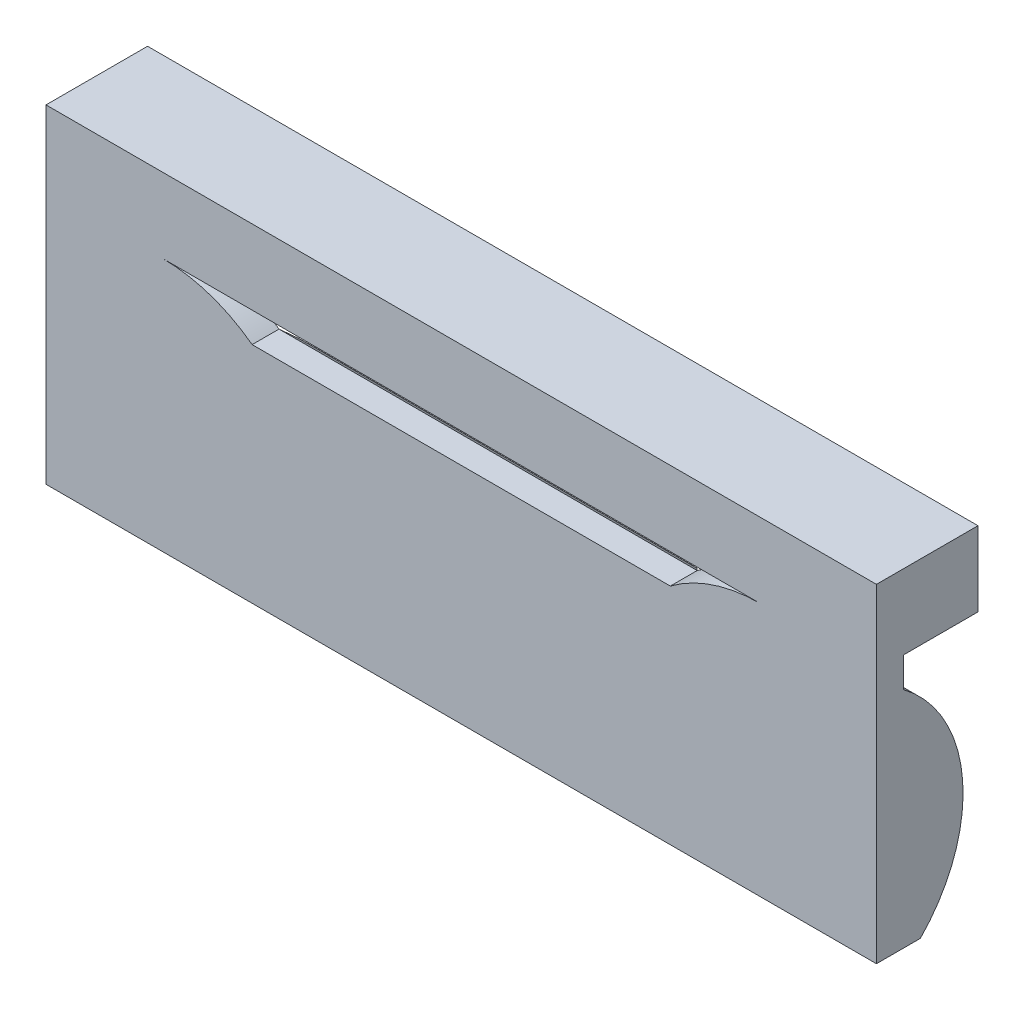
SolidWorks part; units mm, degrees
ref_plane "Front Plane" through (0, 0, 0) normal (0, 0, 1) x (1, 0, 0)
ref_plane "Top Plane" through (0, 0, 0) normal (0, 1, 0) x (1, 0, 0)
ref_plane "Right Plane" through (0, 0, 0) normal (1, 0, 0) x (0, 0, -1)
sketch "Sketch1" plane through (0, 0, 0) normal (0, 0, 1) x (1, 0, 0)
  line L0 (-6.95, 2.25) -> (-6.95, -2.25)
  line L1 (6.5, 2.25) -> (-6.5, 2.25)
  line L2 (6.5, 2.25) -> (6.5, -2.25)
  line L3 (6.5, -2.25) -> (-6.5, -2.25)
  line L4 (-6.5, 2.25) -> (-6.5, -2.25)
  line L5 (6.5, 2.25) -> (-6.5, -2.25) construction
  line L6 (6.5, -2.25) -> (-6.5, 2.25) construction
  line L7 (6.95, 2.25) -> (6.95, -2.25)
  line L8 (6.5, 2.75) -> (-6.5, 2.75)
  line L9 (6.5, -2.75) -> (-6.5, -2.75)
  line L10 (-6.95, 2.25) -> (-6.95, 2.75)
  line L11 (-6.95, 2.75) -> (-6.5, 2.75)
  line L12 (-6.95, -2.25) -> (-6.95, -2.75)
  line L13 (-6.95, -2.75) -> (-6.5, -2.75)
  line L14 (6.5, -2.75) -> (6.95, -2.75)
  line L15 (6.95, -2.75) -> (6.95, -2.25)
  line L16 (6.95, 2.25) -> (6.95, 2.75)
  line L17 (6.95, 2.75) -> (6.5, 2.75)
  line L18 (-5, 1.5) -> (5, 1.5)
  line L20 (-5.835, -2.0198) -> (-5.835, -2.25) construction
  line L21 (0, 2.25) -> (0, -2.25) construction
  line L23 (5.835, 1) -> (5.835, -2.25) construction
  line L24 (-6.5, 1.875) -> (-6.5, 1)
  line L30 (6.5, 1.875) -> (6.5, 1)
  arc A0 (-5, 1.5) -> (-2.8349, -2.25) centre (-5, -1) cw
  arc A1 (5, 1.5) -> (2.8349, -2.25) centre (5, -1) ccw
  point P0 (0, 0)
  point P21 (-4.0978, -2.25)
  point P26 (0, 0)
  dimension "D10" = 2.5
  dimension "D1" = 13
  dimension "D2" = 4.5
  dimension "D7" = 0.75
  dimension "D8" = 10
  dimension "D9" = 0.665
  dimension "D3" = 0.45
  dimension "D4" = 0.45
  dimension "D5" = 0.5
  dimension "D6" = 0.5
extrude "Boss-Extrude1" add sketch "Sketch1" along normal mid plane 0.45 contours L16 L17 L8 L11 L10 L0 L12 L13 L9 L14 L15 L7 L4 L1 L2 L3 | L18 A1 L3 L2 L1 L4 A0 | A1 L18 A0 L3
sketch "Sketch2" plane through (0, 0, -0.225) normal (0, 0, -1) x (-1, 0, 0)
  line L0 (-6.5, 1.875) -> (-6.5, 1) construction
  line L1 (6.5, 1.875) -> (6.5, 1) construction
  line L2 (5, 1.5) -> (-5, 1.5) construction
  line L3 (-6.5, 1.875) -> (-6.5, 1)
  line L4 (6.5, 2.25) -> (-6.5, 2.25)
  line L5 (6.5, -2.25) -> (6.5, 2.25)
  line L6 (-6.5, -2.25) -> (6.5, -2.25)
  line L7 (-6.5, 2.25) -> (-6.5, -2.25)
  line L8 (6.5, 2.25) -> (-6.5, 2.25)
  line L9 (6.5, -2.25) -> (6.5, 2.25)
  line L10 (-6.5, -2.25) -> (6.5, -2.25)
  line L11 (-6.5, 2.25) -> (-6.5, -2.25)
  line L12 (6.5, 1.875) -> (6.5, 1)
  line L13 (5, 1.5) -> (-5, 1.5)
  line L20 (-6.95, -2.25) -> (-6.95, -2.75)
  line L21 (-6.95, 2.25) -> (-6.95, -2.25)
  line L22 (-6.95, 2.75) -> (-6.95, 2.25)
  line L23 (-6.5, 2.75) -> (-6.95, 2.75)
  line L24 (6.5, 2.75) -> (-6.5, 2.75)
  line L25 (6.95, 2.75) -> (6.5, 2.75)
  line L26 (6.95, 2.25) -> (6.95, 2.75)
  line L27 (6.95, -2.25) -> (6.95, 2.25)
  line L28 (6.95, -2.75) -> (6.95, -2.25)
  line L29 (6.5, -2.75) -> (6.95, -2.75)
  line L30 (-6.5, -2.75) -> (6.5, -2.75)
  line L31 (-6.95, -2.75) -> (-6.5, -2.75)
  line L32 (-6.95, -2.25) -> (-6.95, -2.75)
  line L33 (-6.95, 2.25) -> (-6.95, -2.25)
  line L34 (-6.95, 2.75) -> (-6.95, 2.25)
  line L35 (-6.5, 2.75) -> (-6.95, 2.75)
  line L36 (6.5, 2.75) -> (-6.5, 2.75)
  line L37 (6.95, 2.75) -> (6.5, 2.75)
  line L38 (6.95, 2.25) -> (6.95, 2.75)
  line L39 (6.95, -2.25) -> (6.95, 2.25)
  line L40 (6.95, -2.75) -> (6.95, -2.25)
  line L41 (6.5, -2.75) -> (6.95, -2.75)
  line L42 (-6.5, -2.75) -> (6.5, -2.75)
  line L43 (-6.95, -2.75) -> (-6.5, -2.75)
  arc A0 (-2.8349, -2.25) -> (-5, 1.5) centre (-5, -1) ccw construction
  arc A1 (5, 1.5) -> (2.8349, -2.25) centre (5, -1) ccw construction
  arc A2 (-2.8349, -2.25) -> (-5, 1.5) centre (-5, -1) ccw
  arc A3 (5, 1.5) -> (2.8349, -2.25) centre (5, -1) ccw
  line M17 (-6.95, 2.75) -> (-6.95, -2.75)
  line M18 (-6.95, -2.75) -> (6.95, -2.75)
  line M19 (6.95, -2.75) -> (6.95, 2.75)
  line M20 (6.95, 2.75) -> (-6.95, 2.75)
  dimension "D1" = 0
  dimension "D2" = 0
extrude "Boss-Extrude2" add sketch "Sketch2" along normal blind 1.25 contours L11 L8 L9 L10 L3 M20 M17 M18 M19
sketch "Sketch3" plane through (0, 0, -0.225) normal (0, 0, -1) x (-1, 0, 0)
  line L0 (-6.5, 1.875) -> (-6.5, 1) construction
  line L1 (6.5, 1.875) -> (6.5, 1) construction
  line L2 (5, 1.5) -> (-5, 1.5) construction
  line L3 (-6.5, 1.875) -> (-6.5, 1)
  line L4 (6.5, 2.25) -> (-6.5, 2.25)
  line L5 (6.5, -2.25) -> (6.5, 2.25)
  line L6 (-6.5, -2.25) -> (6.5, -2.25)
  line L7 (-6.5, 2.25) -> (-6.5, -2.25)
  line L8 (6.5, 2.25) -> (-6.5, 2.25)
  line L9 (6.5, -2.25) -> (6.5, 2.25)
  line L10 (-6.5, -2.25) -> (6.5, -2.25)
  line L11 (-6.5, 2.25) -> (-6.5, -2.25)
  line L12 (6.5, 1.875) -> (6.5, 1)
  line L13 (5, 1.5) -> (-5, 1.5)
  line L20 (-6.95, -2.25) -> (-6.95, -2.75)
  line L21 (-6.95, 2.25) -> (-6.95, -2.25)
  line L22 (-6.95, 2.75) -> (-6.95, 2.25)
  line L23 (-6.5, 2.75) -> (-6.95, 2.75)
  line L24 (6.5, 2.75) -> (-6.5, 2.75)
  line L25 (6.95, 2.75) -> (6.5, 2.75)
  line L26 (6.95, 2.25) -> (6.95, 2.75)
  line L27 (6.95, -2.25) -> (6.95, 2.25)
  line L28 (6.95, -2.75) -> (6.95, -2.25)
  line L29 (6.5, -2.75) -> (6.95, -2.75)
  line L30 (-6.5, -2.75) -> (6.5, -2.75)
  line L31 (-6.95, -2.75) -> (-6.5, -2.75)
  line L32 (-6.95, -2.25) -> (-6.95, -2.75)
  line L33 (-6.95, 2.25) -> (-6.95, -2.25)
  line L34 (-6.95, 2.75) -> (-6.95, 2.25)
  line L35 (-6.5, 2.75) -> (-6.95, 2.75)
  line L36 (6.5, 2.75) -> (-6.5, 2.75)
  line L37 (6.95, 2.75) -> (6.5, 2.75)
  line L38 (6.95, 2.25) -> (6.95, 2.75)
  line L39 (6.95, -2.25) -> (6.95, 2.25)
  line L40 (6.95, -2.75) -> (6.95, -2.25)
  line L41 (6.5, -2.75) -> (6.95, -2.75)
  line L42 (-6.5, -2.75) -> (6.5, -2.75)
  line L43 (-6.95, -2.75) -> (-6.5, -2.75)
  arc A0 (-2.8349, -2.25) -> (-5, 1.5) centre (-5, -1) ccw construction
  arc A1 (5, 1.5) -> (2.8349, -2.25) centre (5, -1) ccw construction
  arc A2 (-2.8349, -2.25) -> (-5, 1.5) centre (-5, -1) ccw
  arc A3 (5, 1.5) -> (2.8349, -2.25) centre (5, -1) ccw
  dimension "D1" = 0
  dimension "D2" = 0
extrude "Boss-Extrude3" add sketch "Sketch3" along normal blind 2 contours A3 L13 A2 L10
sketch "Sketch4" plane through (0, 0, -2.225) normal (0, 0, -1) x (-1, 0, 0)
  line L0 (5, 1.5) -> (-5, 1.5) construction
  line L1 (3.5, -2.25) -> (-3.5, -2.25)
  line L2 (3.5, -2.25) -> (3.5, 2.25)
  line L3 (3.5, 2.25) -> (-3.5, 2.25)
  line L4 (-3.5, -2.25) -> (-3.5, 2.25)
  line L5 (3.5, -2.25) -> (-3.5, 2.25) construction
  line L6 (3.5, 2.25) -> (-3.5, -2.25) construction
  line L7 (-3.5, 1) -> (3.5, 1)
  line L8 (5, 1.5) -> (-5, 1.5)
  arc A0 (5, 1.5) -> (2.8349, -2.25) centre (5, -1) ccw construction
  arc A1 (-2.8349, -2.25) -> (-5, 1.5) centre (-5, -1) ccw construction
  arc A2 (5, 1.5) -> (2.8349, -2.25) centre (5, -1) ccw
  arc A3 (-2.8349, -2.25) -> (-5, 1.5) centre (-5, -1) ccw
  point P0 (0, 0)
  arc M5 (2.8349, -2.25) -> (5, 1.5) centre (5, -1) cw
  line M6 (5, 1.5) -> (-5, 1.5)
  arc M7 (-5, 1.5) -> (-2.8349, -2.25) centre (-5, -1) cw
  dimension "D1" = 4.5
  dimension "D2" = 7
  dimension "D3" = 0.75
extrude "Cut-Extrude1" cut sketch "Sketch4" against normal through all contours L4 L7 L2 M6 | L2 M5 M6 | L4 M7 M6
sketch "Sketch5" plane through (0, 0, 0) normal (1, 0, 0) x (0, 0, -1)
  line L0 (-1.275, 1.5) -> (3.725, 1.5)
  line L1 (-1.275, -3.5) -> (3.725, -3.5)
  line L2 (3.725, 1.5) -> (3.725, -3.5)
  line L4 (0.225, 1.5) -> (-0.225, 1.5)
  line L5 (-0.225, 1.5) -> (-0.225, 1)
  line L6 (-0.225, 1) -> (0.225, 1)
  line L7 (0.225, 1) -> (0.225, 1.5)
  line L8 (0.225, 1.5) -> (-0.225, 1.5)
  line L9 (-0.225, 1.5) -> (-0.225, 1)
  line L10 (-0.225, 1) -> (0.225, 1)
  line L11 (0.225, 1) -> (0.225, 1.5)
  arc A0 (-1.275, 1.5) -> (-1.275, -3.5) centre (-1.275, -1) cw
  dimension "D2" = 2.5
  dimension "D3" = 5
  dimension "D1" = 0
extrude "Cut-Extrude2" cut sketch "Sketch5" against normal through all both and the other way through all
